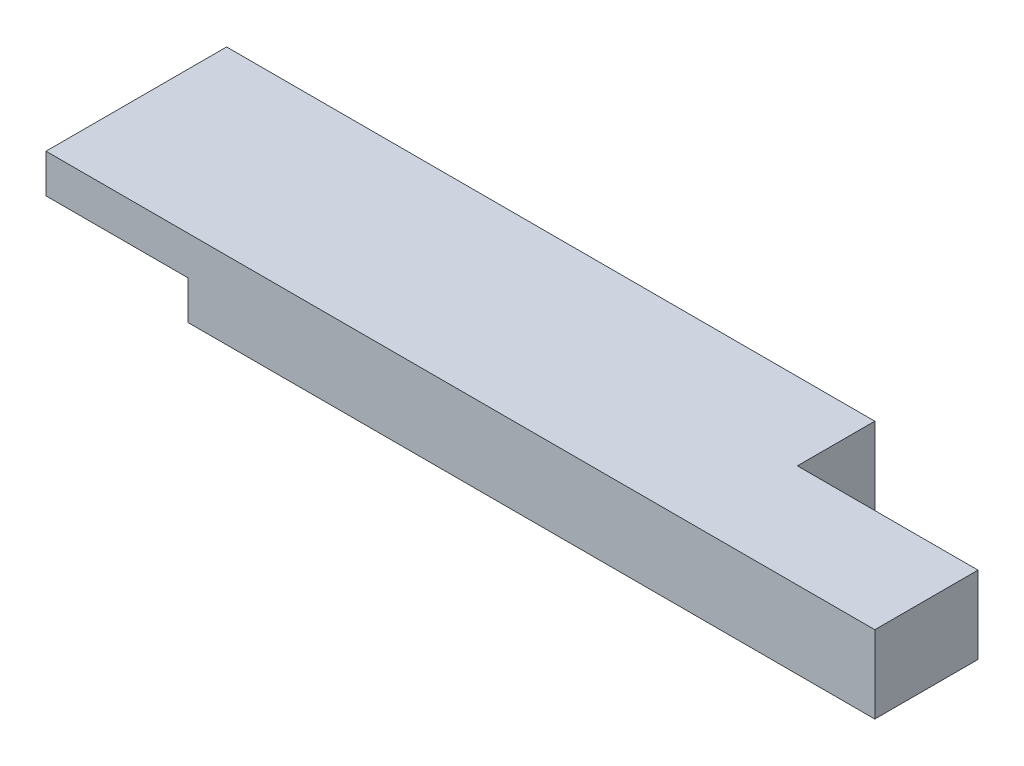
SolidWorks part; units mm, degrees
material "Pine"
ref_plane "Front Plane" through (0, 0, 0) normal (0, 0, 1) x (1, 0, 0)
ref_plane "Top Plane" through (0, 0, 0) normal (0, 1, 0) x (1, 0, 0)
ref_plane "Right Plane" through (0, 0, 0) normal (1, 0, 0) x (0, 0, -1)
sketch "Sketch1" plane through (0, 0, 0) normal (0, 1, 0) x (1, 0, 0)
  line L1 (0, 0) -> (407.9875, 0)
  line L2 (0, 0) -> (0, 88.9)
  line L3 (0, 88.9) -> (407.9875, 88.9)
  line L4 (407.9875, 0) -> (407.9875, 88.9)
  dimension "D1" = 88.9
  dimension "D2" = 407.9875
extrude "Boss-Extrude1" add sketch "Sketch1" along normal blind 38.1
sketch "Sketch3" plane through (0, 38.1, 0) normal (0, 1, 0) x (1, 0, 0)
  line L1 (407.9875, 88.9) -> (319.0875, 88.9)
  line L2 (407.9875, 88.9) -> (407.9875, 50.8)
  line L3 (407.9875, 50.8) -> (319.0875, 50.8)
  line L4 (319.0875, 88.9) -> (319.0875, 50.8)
  dimension "D1" = 88.9
  dimension "D2" = 38.1
extrude "Cut-Extrude2" cut sketch "Sketch3" against normal through all
sketch "Sketch4" plane through (0, 0, 0) normal (0, 0, 1) x (1, 0, 0)
  line L1 (0, 0) -> (69.85, 0)
  line L2 (0, 0) -> (0, 19.05)
  line L3 (0, 19.05) -> (69.85, 19.05)
  line L4 (69.85, 0) -> (69.85, 19.05)
  dimension "D1" = 19.05
  dimension "D2" = 69.85
extrude "Cut-Extrude3" cut sketch "Sketch4" against normal through all contours L3 L4 L1 L2
